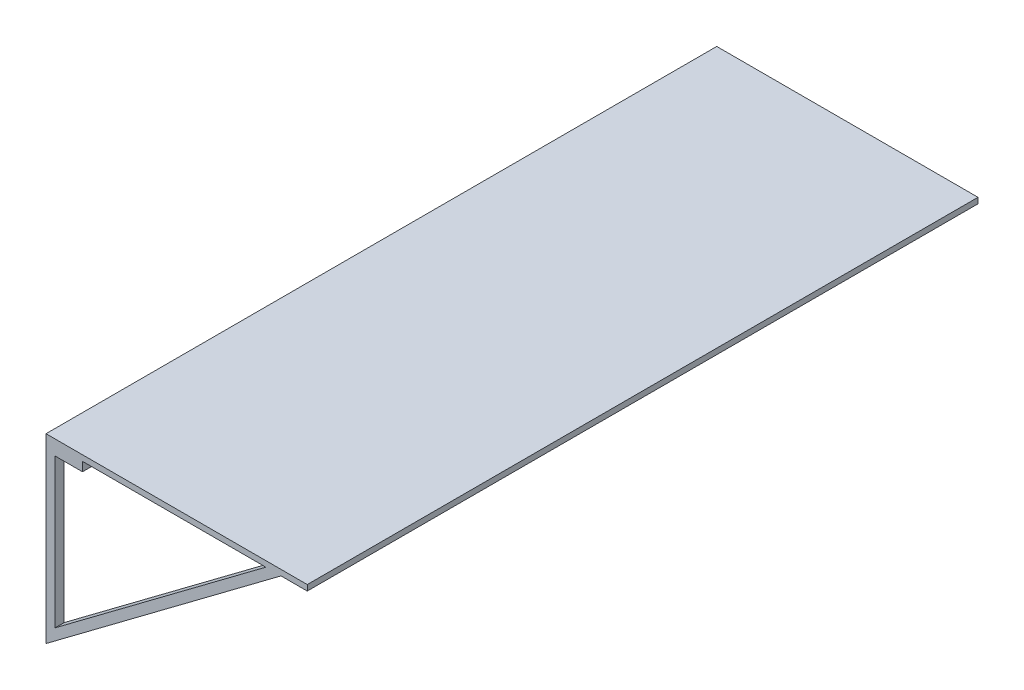
SolidWorks part; units mm, degrees
ref_plane "Front Plane" through (0, 0, 0) normal (0, 0, 1) x (1, 0, 0)
ref_plane "Top Plane" through (0, 0, 0) normal (0, 1, 0) x (1, 0, 0)
ref_plane "Right Plane" through (0, 0, 0) normal (1, 0, 0) x (0, 0, -1)
sketch "Sketch1" plane through (0, 0, 0) normal (0, 0, 1) x (1, 0, 0)
  line L0 (730.25, 492.125) -> (656.8172, 492.125)
  line L1 (101.9818, 492.125) -> (101.9818, 466.725)
  line L2 (0, 0) -> (0, 508)
  line L3 (0, 508) -> (730.25, 508)
  line L4 (730.25, 492.125) -> (730.25, 508)
  line L5 (0, 0) -> (656.8172, 492.125)
  line L7 (614.457, 492.125) -> (25.4, 50.7698)
  line L8 (101.9818, 466.725) -> (25.4, 466.725)
  line L9 (25.4, 466.725) -> (25.4, 50.7698)
  line L10 (614.457, 492.125) -> (101.9818, 492.125)
  dimension "D1" = 730.25
  dimension "D2" = 508
  dimension "D3" = 25.4
  dimension "D4" = 15.875
  dimension "D5" = 25.4
  dimension "D6" = 25.4
extrude "Boss-Extrude1" add sketch "Sketch1" along normal blind 1874.774
sketch "Sketch2" plane through (730.25, 0, 0) normal (1, 0, 0) x (0, 0, -1)
  line L0 (-1874.774, 492.125) -> (0, 492.125) construction
  line L1 (-1849.374, 492.125) -> (-950.087, 492.125)
  line L2 (-1849.374, 492.125) -> (-1849.374, 0)
  line L3 (-1849.374, 0) -> (-950.087, 0)
  line L4 (-950.087, 492.125) -> (-950.087, 0)
  line L5 (-1874.774, 0) -> (0, 0) construction
  line L6 (0, 0) -> (0, 492.125) construction
  line L7 (-924.687, 492.125) -> (-25.4, 492.125)
  line L8 (-924.687, 492.125) -> (-924.687, 0)
  line L9 (-924.687, 0) -> (-25.4, 0)
  line L10 (-25.4, 492.125) -> (-25.4, 0)
  line L11 (-1874.774, 0) -> (-1874.774, 492.125) construction
  dimension "D1" = 25.4
  dimension "D2" = 25.4
  dimension "D3" = 899.287
  dimension "D4" = 899.287
extrude "Cut-Extrude1" cut sketch "Sketch2" against normal through all
